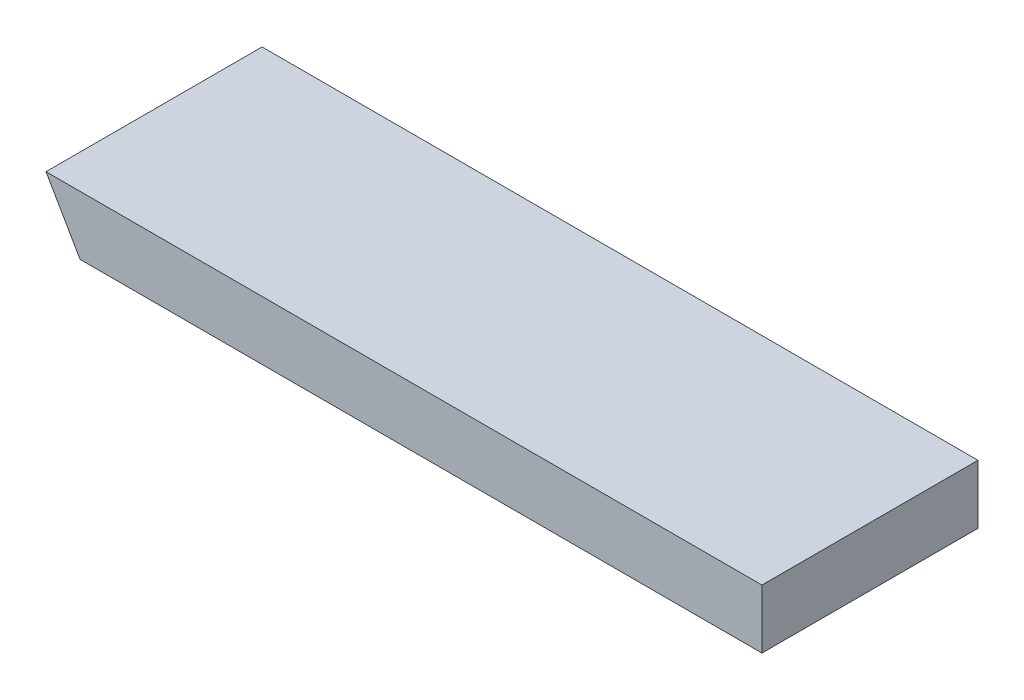
SolidWorks part; units mm, degrees
ref_plane "Front Plane" through (0, 0, 0) normal (0, 0, 1) x (1, 0, 0)
ref_plane "Top Plane" through (0, 0, 0) normal (0, 1, 0) x (1, 0, 0)
ref_plane "Right Plane" through (0, 0, 0) normal (1, 0, 0) x (0, 0, -1)
sketch "Sketch1" plane through (0, 0, 0) normal (0, 1, 0) x (1, 0, 0)
  line L1 (0, 0) -> (508, 0)
  line L2 (0, 0) -> (0, 139.7)
  line L3 (0, 139.7) -> (508, 139.7)
  line L4 (508, 0) -> (508, 139.7)
  dimension "D1" = 139.7
  dimension "D2" = 508
extrude "Boss-Extrude1" add sketch "Sketch1" along normal blind 38.1
sketch "Sketch2" plane through (0, 0, 0) normal (0, 0, 1) x (1, 0, 0)
  line L0 (45.0879, 38.1) -> (67.085, 0)
  line L1 (0, 0) -> (508, 0) construction
  line L2 (45.0879, 38.1) -> (105.2145, -66.0424) construction
  line L3 (67.085, 0) -> (0, 0)
  line L4 (0, 0) -> (0, 38.1)
  line L5 (0, 38.1) -> (45.0879, 38.1)
extrude "Cut-Extrude1" cut sketch "Sketch2" against normal through all
